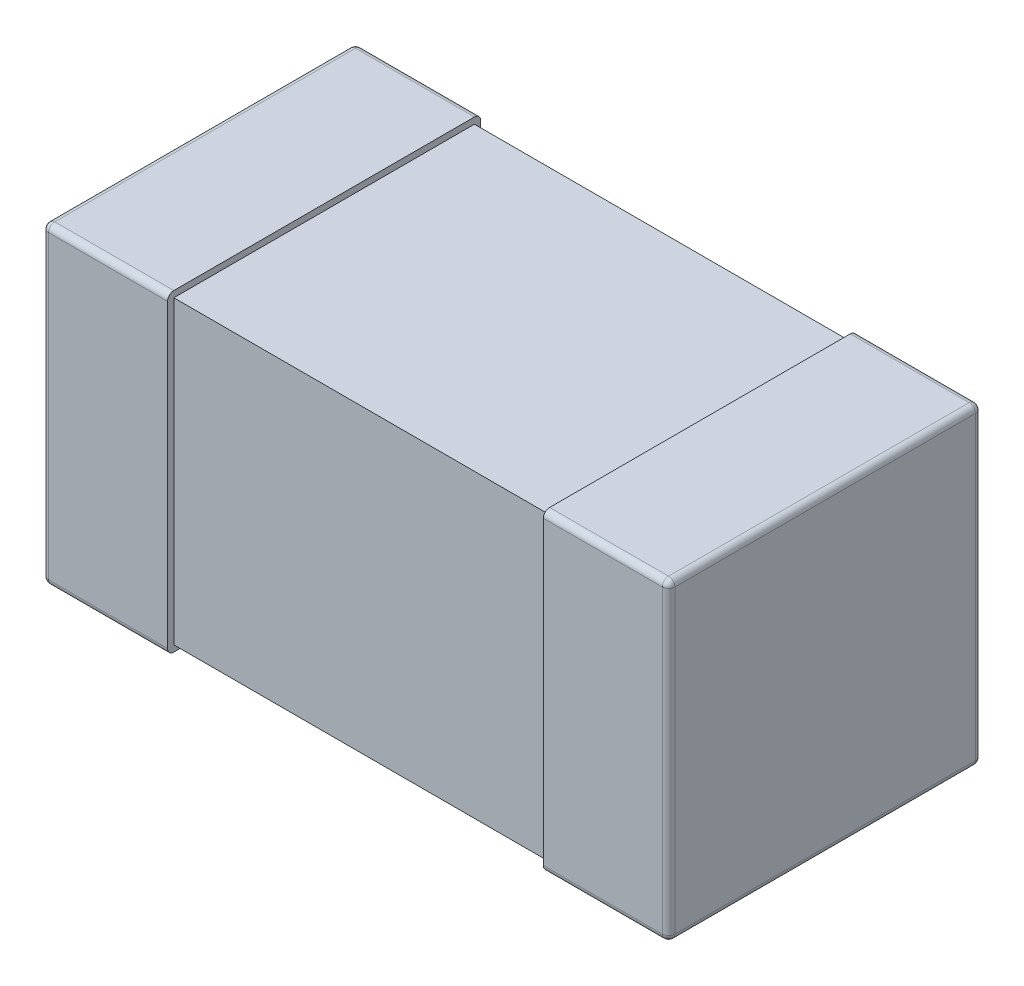
SolidWorks part; units mm, degrees
ref_plane "Front Plane" through (0, 0, 0) normal (0, 0, 1) x (1, 0, 0)
ref_plane "Top Plane" through (0, 0, 0) normal (0, 1, 0) x (1, 0, 0)
ref_plane "Right Plane" through (0, 0, 0) normal (1, 0, 0) x (0, 0, -1)
sketch "Sketch1" plane through (0, 0, 0) normal (0, 1, 0) x (1, 0, 0)
  line L0 (0, 0.15) -> (0, -0.15) construction
  line L1 (-0.5, 0) -> (0, 0) construction
  line L3 (-0.5, 0.25) -> (-0.3, 0.25)
  line L4 (-0.5, 0.25) -> (-0.5, -0.25)
  line L5 (-0.5, -0.25) -> (-0.3, -0.25)
  line L6 (-0.3, 0.25) -> (-0.3, -0.25)
  dimension "BANDWIDTH" = 0.2
  dimension "WIDTH" = 0.5
  dimension "LENGTH-HALF" = 0.5
extrude "THICKNESS" add sketch "Sketch1" along normal mid plane 0.5
fillet "Fillet1" radius 0.01 8 edges at (-0.5, -0.25, 0) (-0.4, -0.25, -0.25) (-0.5, 0, -0.25) (-0.4, -0.25, 0.25) (-0.5, 0, 0.25) (-0.5, 0.25, 0) (-0.4, 0.25, -0.25) (-0.4, 0.25, 0.25)
sketch "Sketch2" plane through (0, 0, 0) normal (1, 0, 0) x (0, 0, -1)
  line L0 (0, 0.25) -> (0, -0.25) construction
  line L1 (-0.24, 0.24) -> (0.24, 0.24)
  line L2 (-0.24, 0.24) -> (-0.24, -0.24)
  line L3 (-0.24, -0.24) -> (0.24, -0.24)
  line L4 (0.24, 0.24) -> (0.24, -0.24)
  line L5 (-0.24, 0.25) -> (0.24, 0.25) construction
  line L6 (-0.24, -0.25) -> (0.24, -0.25) construction
  line L7 (-0.25, 0) -> (0.25, 0) construction
  line L8 (-0.25, 0.24) -> (-0.25, -0.24) construction
  line L9 (0.25, 0.24) -> (0.25, -0.24) construction
  dimension "D1" = 0.01
  dimension "D2" = 0.01
extrude "Boss-Extrude2" add sketch "Sketch2" against normal up to surface (0.3 mm away) up to face at (-0.3, 0, 0)
mirror "Mirror3" about plane through (0, 0, 0) normal (1, 0, 0) of "Boss-Extrude2", "Fillet1", "THICKNESS"
